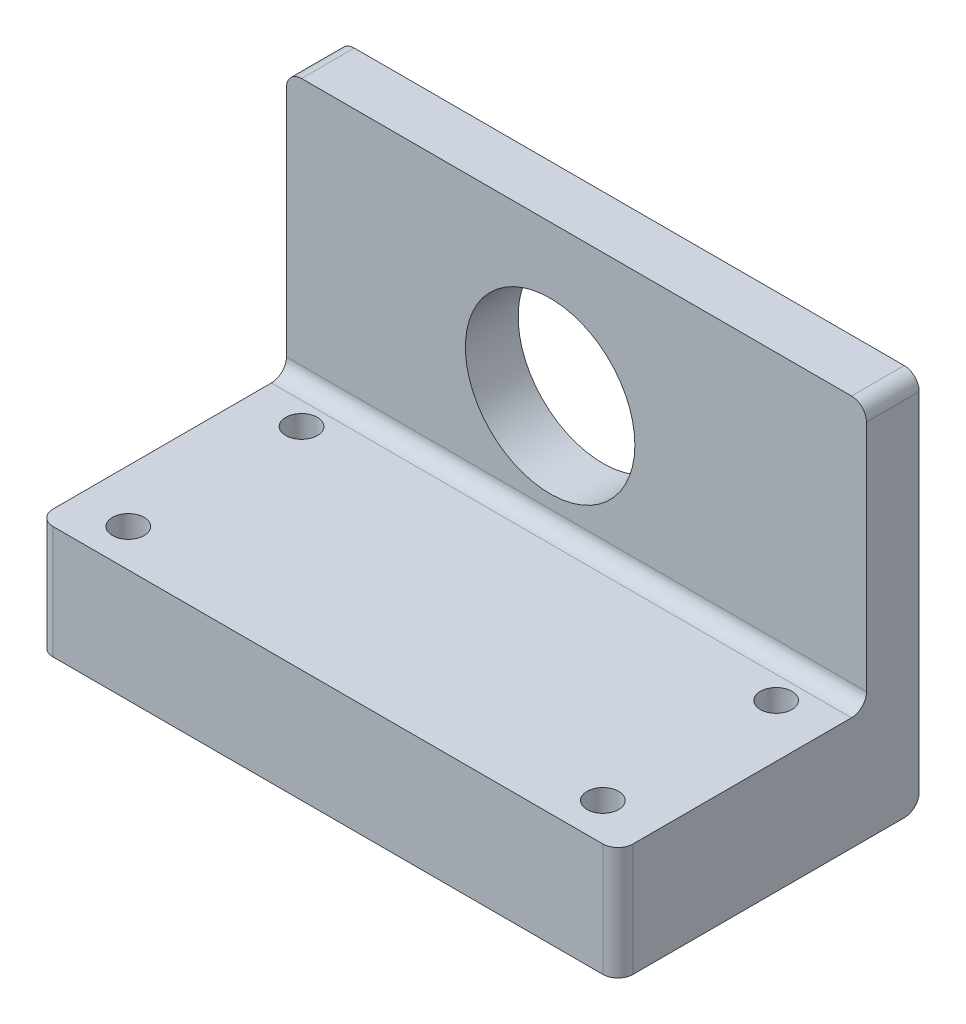
SolidWorks part; units mm, degrees
ref_plane "Front Plane" through (0, 0, 0) normal (0, 0, 1) x (1, 0, 0)
ref_plane "Top Plane" through (0, 0, 0) normal (0, 1, 0) x (1, 0, 0)
ref_plane "Right Plane" through (0, 0, 0) normal (1, 0, 0) x (0, 0, -1)
sketch "Sketch1" plane through (0, 0, 0) normal (0, 0, 1) x (1, 0, 0)
  line L1 (-35, 17.5) -> (42, 17.5)
  line L2 (-35, 17.5) -> (-35, -17.5)
  line L3 (-35, -17.5) -> (42, -17.5)
  line L4 (42, 17.5) -> (42, -17.5)
  dimension "D1" = 77
  dimension "D2" = 35
  dimension "D3" = 17.5
  dimension "D4" = 35
extrude "Boss-Extrude1" add sketch "Sketch1" along normal blind 7
sketch "Sketch2" plane through (0, 0, 7) normal (0, 0, 1) x (1, 0, 0)
  line L2 (42, -17.5) -> (42, 17.5) construction
  line L3 (42, 17.5) -> (-35, 17.5) construction
  circle A0 centre (0, -2.5) radius 11.25
  point P3 (0, 0)
  dimension "D1" = 42
  dimension "D2" = 22.5
  dimension "D3" = 20
extrude "Cut-Extrude1" cut sketch "Sketch2" against normal blind 15
sketch "Sketch3" plane through (0, 0, 0) normal (0, 0, -1) x (-1, 0, 0)
  line L0 (35, 17.5) -> (35, -17.5) construction
  line L1 (-42, -17.5) -> (35, -17.5)
  line L2 (-42, -17.5) -> (-42, -32.5)
  line L3 (-42, -32.5) -> (35, -32.5)
  line L4 (35, -17.5) -> (35, -32.5)
  dimension "D1" = 15
extrude "Boss-Extrude2" add sketch "Sketch3" against normal blind 40
sketch "Sketch4" plane through (0, -17.5, 0) normal (0, 1, 0) x (1, 0, 0)
  line L0 (42, -40) -> (42, -7) construction
  line L1 (-35, -40) -> (-35, -7) construction
  line L2 (-35, -40) -> (42, -40) construction
  line L3 (-35, -7) -> (42, -7) construction
  circle A0 centre (-28, -35) radius 2.1
  circle A1 centre (-28, -12) radius 2.1
  circle A2 centre (35, -35) radius 2.1
  circle A3 centre (35, -12) radius 2.1
  point P14 (0, 0)
  dimension "D1" = 4.2
  dimension "D2" = 4.2
  dimension "D3" = 4.2
  dimension "D4" = 4.2
  dimension "D5" = 7
  dimension "D6" = 7
  dimension "D7" = 7
  dimension "D8" = 7
  dimension "D9" = 5
  dimension "D10" = 5
  dimension "D11" = 5
extrude "Cut-Extrude2" cut sketch "Sketch4" against normal blind 20
fillet "Fillet1" radius 2 1 edges at (3.5, -17.5, 7)
fillet "Fillet2" radius 2 5 edges at (-35, 17.5, 3.5) (42, 17.5, 3.5) (42, -25, 40) (-35, -25, 40) (3.5, -32.5, 0)
